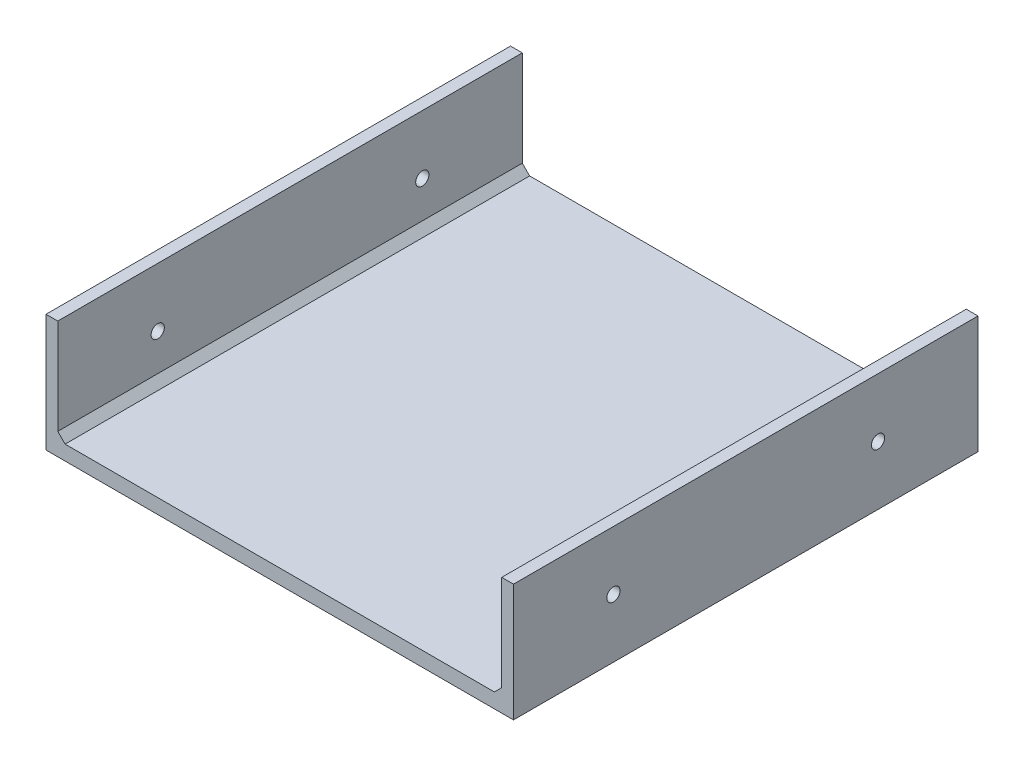
SolidWorks part; units mm, degrees
ref_plane "Front Plane" through (0, 0, 0) normal (0, 0, 1) x (1, 0, 0)
ref_plane "Top Plane" through (0, 0, 0) normal (0, 1, 0) x (1, 0, 0)
ref_plane "Right Plane" through (0, 0, 0) normal (1, 0, 0) x (0, 0, -1)
sketch "Sketch1" plane through (0, 0, 0) normal (0, 1, 0) x (1, 0, 0)
  line L1 (-79.5, 0) -> (79.5, 0)
  line L2 (-79.5, 0) -> (-79.5, -158)
  line L3 (-79.5, -158) -> (79.5, -158)
  line L4 (79.5, 0) -> (79.5, -158)
  point P4 (0, 0)
  dimension "D1" = 159
  dimension "D2" = 158
extrude "Boss-Extrude1" add sketch "Sketch1" along normal blind 5
sketch "Sketch2" plane through (0, 0, 0) normal (0, -1, 0) x (1, 0, 0)
  line L0 (-79.5, 0) -> (-79.5, 158) construction
  line L1 (79.5, 0) -> (-79.5, 0) construction
  line L2 (79.5, 0) -> (79.5, 40) construction
  line L3 (79.5, 40) -> (-79.5, 40) construction
  line L4 (-79.5, 0) -> (-79.5, 40) construction
  line L5 (79.5, 20) -> (0, 20) construction
  line L6 (0, 40) -> (0, 0) construction
  line L7 (0, 20) -> (-79.5, 20) construction
  point P12 (39.75, 20)
  point P14 (-39.75, 20)
  dimension "D1" = 40
hole_wizard "CBORE for M4 SHCS1" [suppressed] positions "Sketch2" profile "Sketch3" counterbore size "M4" standard "ANSI Metric"
sketch "Sketch3" plane through (-18.75, 0, 20) normal (1, 0, 0) x (0, 0, -1)
  line L0 (0, 0) -> (0, 5)
  line L1 (0, 5) -> (2.25, 5)
  line L3 (2.25, 5) -> (2.25, 4)
  line L4 (2.25, 4) -> (4, 4)
  line L5 (4, 4) -> (4, 0)
  line L7 (4, 0) -> (0, 0)
  line L11 (0, -6.35) -> (0, 107.95) construction
  dimension "Thru Hole Dia." = 4.5
  dimension "Thru Hole Depth" = 5
  dimension "C'Bore Dia." = 8
  dimension "C'Bore Depth" = 4
sketch "Sketch4" plane through (0, 5, 0) normal (0, 1, 0) x (1, 0, 0)
  line L13 (79.5, 0) -> (-79.5, 0) construction
  line L15 (79.5, -158) -> (75.5, -158)
  line L16 (79.5, -158) -> (79.5, 0)
  line L17 (79.5, 0) -> (75.5, 0)
  line L18 (75.5, -158) -> (75.5, 0)
  dimension "D1" = 4
extrude "Boss-Extrude2" add sketch "Sketch4" along normal blind 35
sketch "Sketch8" plane through (75.5, 0, 0) normal (-1, 0, 0) x (0, 0, 1)
  line L13 (79, 40) -> (79, 20) construction
  line L14 (0, 40) -> (158, 40) construction
  line L16 (79, 20) -> (34, 20) construction
  point P42 (34, 20)
  point P44 (124, 20)
  dimension "D1" = 20
  dimension "D2" = 90
hole_wizard "M4 Clearance Hole1" positions "Sketch8" profile "Sketch9" hole size "M4" standard "ANSI Metric" end condition through all
sketch "Sketch9" plane through (75.5, 20, 124) normal (0, 1, 0) x (0, 0, 1)
  line L0 (0, 0) -> (0, 4)
  line L1 (0, 4) -> (2.25, 4)
  line L2 (2.25, 4) -> (2.25, 0)
  line L5 (2.25, 0) -> (0, 0)
  line L11 (0, -6.35) -> (0, 107.95) construction
  dimension "Thru Hole Dia." = 4.5
  dimension "Thru Hole Depth" = 4
sketch "Sketch10" plane through (0, 5, 0) normal (0, 1, 0) x (1, 0, 0)
  line L0 (-79.5, 0) -> (-79.5, -158) construction
  line L1 (79.5, -158) -> (-79.5, 0) construction
  circle A0 centre (50.5, -129.1824) radius 10
  dimension "D2" = 20
  dimension "D1" = 130
extrude "Cut-Extrude2" [suppressed] cut sketch "Sketch10" against normal up to next
ref_plane "Plane2" through (0, 0, 0) normal (-1, 0, 0) x (0, 0, 1)
mirror "Mirror2" about plane through (0, 0, 0) normal (-1, 0, 0) of "M4 Clearance Hole1", "Boss-Extrude2"
sketch "Sketch13" plane through (0, 5, 0) normal (0, 1, 0) x (1, 0, 0)
  line L1 (-79.5, -158) -> (-4.5, -158)
  line L2 (-79.5, -158) -> (-79.5, -143)
  line L3 (-79.5, -143) -> (-4.5, -143)
  line L4 (-4.5, -158) -> (-4.5, -143)
  dimension "D1" = 75
  dimension "D2" = 15
extrude "Cut-Extrude4" [suppressed] cut sketch "Sketch13" against normal through all and the other way through all
sketch "Sketch14" [suppressed] plane through (0, 5, 0) normal (0, 1, 0) x (1, 0, 0)
  line L0 (-73.75, 0) -> (-73.75, -143) construction
  line L5 (-4.75, -143) -> (-4.75, -158)
  line L6 (-4.75, -158) -> (73.75, -158)
  line L7 (73.75, -158) -> (73.75, -155)
  line L8 (73.75, 0) -> (73.75, -158) construction
  line L9 (73.75, -155) -> (-1.75, -155)
  line L12 (-4.75, -158) -> (73.75, -158) construction
  line L13 (-73.75, -140) -> (-1.75, -140)
  line L14 (-73.75, -140) -> (-73.75, -143)
  line L15 (-73.75, -143) -> (-4.75, -143)
  line L17 (-1.75, -140) -> (-1.75, -155)
  line L18 (-4.75, -143) -> (-73.75, -143) construction
  dimension "D1" = 3
  dimension "D2" = 3
  dimension "D3" = 3
extrude "Boss-Extrude4" [suppressed] add sketch "Sketch14" along normal blind 5
fillet "Fillet1" [suppressed] radius 2.5
sketch "Sketch15" [suppressed] plane through (0, 5, 0) normal (0, 1, 0) x (1, 0, 0)
  line L0 (53.75, -24.2516) -> (53.75, -92.815) construction
  line L1 (73.75, 0) -> (73.75, -152.5) construction
  line L2 (71.25, 0) -> (-71.25, 0) construction
  circle A0 centre (53.75, -30) radius 3.05
  circle A1 centre (53.75, -80) radius 3.05
  dimension "D2" = 6.1
  dimension "D3" = 50
  dimension "D1" = 20
  dimension "D4" = 30
extrude "Cut-Extrude5" [suppressed] cut sketch "Sketch15" against normal blind 3.1
pattern_linear "LPattern1" [suppressed] count 2 spacing 30
mirror "Mirror3" [suppressed] about plane through (0, 0, 0) normal (-1, 0, 0)
chamfer "Chamfer1" [suppressed] distance 0.25 angle 45
chamfer "Chamfer2" distance 2.5 angle 45 2 edges at (75.5, 5, 79) (-75.5, 5, 79)
equation "\"D2@Sketch14\"=\"D1@Sketch14\""
equation "\"D3@Sketch14\"=\"D1@Sketch14\""
